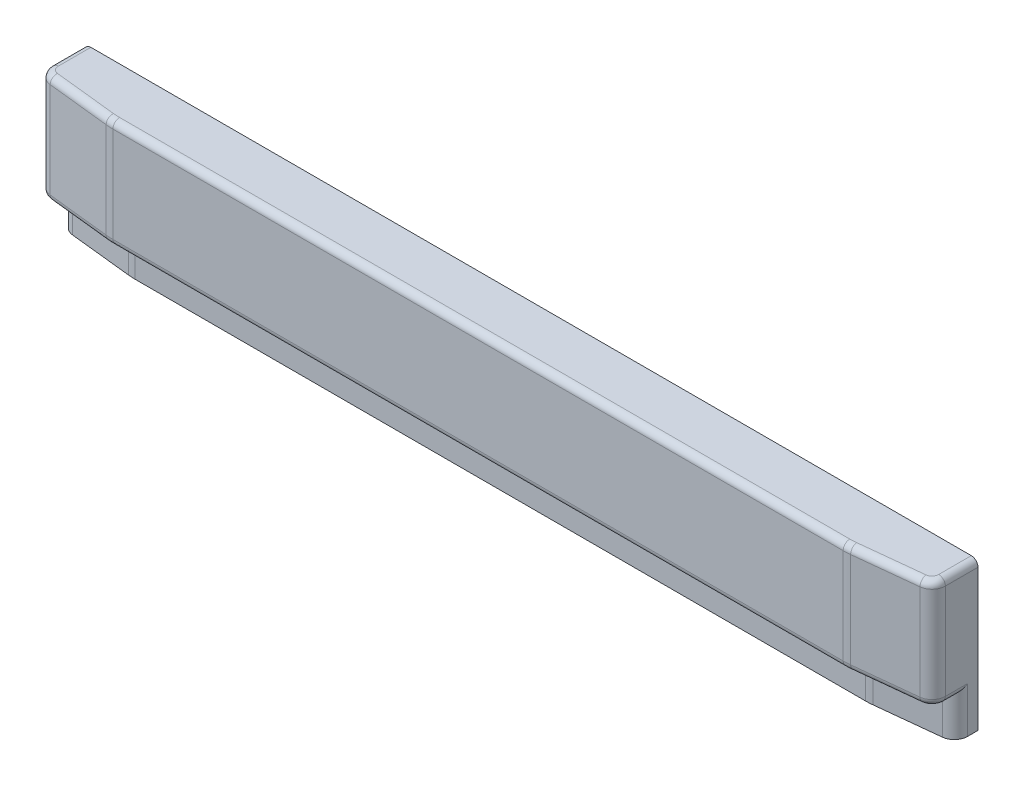
SolidWorks part; units mm, degrees
other "Camera1"
ref_plane "Front Plane" through (0, 0, 0) normal (0, 0, 1) x (1, 0, 0)
ref_plane "Top Plane" through (0, 0, 0) normal (0, 1, 0) x (1, 0, 0)
ref_plane "Right Plane" through (0, 0, 0) normal (1, 0, 0) x (0, 0, -1)
sketch "Sketch7" plane through (0, 0, 0) normal (0, 1, 0) x (1, 0, 0)
  line L0 (0, 0) -> (1016, 0)
  line L1 (1016, 0) -> (1016, -50.8)
  line L2 (1016, -50.8) -> (927.1, -60.325)
  line L3 (927.1, -60.325) -> (88.9, -60.325)
  line L4 (88.9, -60.325) -> (0, -50.8)
  line L5 (0, -50.8) -> (0, 0)
  dimension "D1" = 1016
  dimension "D2" = 50.8
  dimension "D3" = 88.9
  dimension "D4" = 88.9
  dimension "D5" = 60.325
extrude "Boss-Extrude1" add sketch "Sketch7" along normal blind 168.275
ref_plane "Wall Plane" through (0, 0, 0) normal (0, 0, 1) x (1, 0, 0)
ref_plane "Floor Plane" through (0, 0, 0) normal (0, 1, 0) x (1, 0, 0)
sketch "Sketch10" plane through (0, 0, 0) normal (0, -1, 0) x (1, 0, 0)
  line L0 (0, 50.8) -> (0, 25.4)
  line L1 (0, 0) -> (0, 50.8) construction
  line L2 (0, 25.4) -> (88.9, 34.925)
  line L3 (88.9, 34.925) -> (927.1, 34.925)
  line L4 (927.1, 34.925) -> (1016, 25.4)
  line L5 (1016, 50.8) -> (1016, 0) construction
  line L6 (1016, 25.4) -> (1016, 50.8)
  line L7 (1016, 50.8) -> (927.1, 60.325)
  line L8 (927.1, 60.325) -> (88.9, 60.325)
  line L9 (88.9, 60.325) -> (0, 50.8)
  dimension "D1" = 25.4
extrude "Cut-Extrude1" cut sketch "Sketch10" against normal blind 44.45
fillet "Fillet1" radius 15.24 4 edges at (1016, 22.225, 25.4) (1016, 106.3625, 50.8) (0, 22.225, 25.4) (0, 106.3625, 50.8)
fillet "Fillet2" radius 76.2 4 edges at (927.1, 22.225, 34.925) (927.1, 106.3625, 60.325) (88.9, 22.225, 34.925) (88.9, 106.3625, 60.325)
fillet "Fillet3" radius 7.62 9 edges at (0, 168.275, 18.5528) (3.9042, 168.275, 47.2918) (49.2346, 168.275, 56.0751) (88.9058, 168.275, 60.2165) (1016, 168.275, 18.5528) (1012.0958, 168.275, 47.2918) (966.7654, 168.275, 56.0751) (927.0942, 168.275, 60.2165) (508, 168.275, 60.325)
fillet "Fillet4" radius 7.62 9 edges at (1016, 44.45, 24.4056) (1012.0958, 44.45, 47.2918) (966.7654, 44.45, 56.0751) (927.0942, 44.45, 60.2165) (0, 44.45, 24.4056) (3.9042, 44.45, 47.2918) (49.2346, 44.45, 56.0751) (88.9058, 44.45, 60.2165) (508, 44.45, 60.325)
